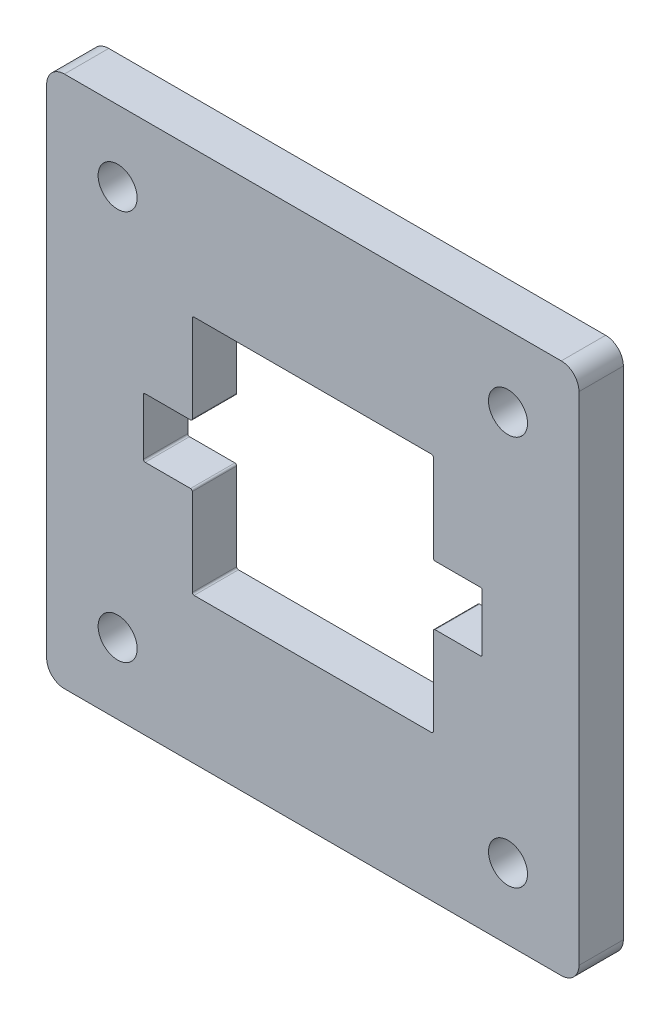
SolidWorks part; units mm, degrees
ref_plane "Front Plane" through (0, 0, 0) normal (0, 0, 1) x (1, 0, 0)
ref_plane "Top Plane" through (0, 0, 0) normal (0, 1, 0) x (1, 0, 0)
ref_plane "Right Plane" through (0, 0, 0) normal (1, 0, 0) x (0, 0, -1)
sketch "Sketch1" plane through (0, 0, 0) normal (0, 0, 1) x (1, 0, 0)
  line L0 (10.425, 10.425) -> (10.425, 16.925)
  line L1 (10.425, 16.925) -> (6.925, 16.925)
  line L2 (6.925, 16.925) -> (6.925, 21.175)
  line L3 (6.925, 21.175) -> (10.425, 21.175)
  line L4 (10.425, 21.175) -> (10.425, 27.675)
  line L5 (10.425, 27.675) -> (27.675, 27.675)
  line L6 (27.675, 27.675) -> (27.675, 21.175)
  line L7 (27.675, 16.925) -> (31.175, 16.925)
  line L8 (31.175, 16.925) -> (31.175, 21.175)
  line L9 (27.675, 21.175) -> (31.175, 21.175)
  line L10 (27.675, 16.925) -> (27.675, 10.425)
  line L11 (27.675, 10.425) -> (10.425, 10.425)
  line L12 (19.05, 27.675) -> (19.05, 10.425) construction
  line L13 (31.175, 19.05) -> (6.925, 19.05) construction
  line L14 (19.05, 38.1) -> (19.05, 0) construction
  line L15 (0, 0) -> (38.1, 0)
  line L16 (0, 0) -> (0, 38.1)
  line L17 (0, 38.1) -> (38.1, 38.1)
  line L18 (38.1, 0) -> (38.1, 38.1)
  line L19 (38.1, 19.05) -> (0, 19.05) construction
  point P17 (19.05, 19.05)
  point P18 (19.05, 19.05)
  dimension "D1" = 17.25
  dimension "D2" = 17.25
  dimension "D3" = 24.25
  dimension "D4" = 4.25
  dimension "D5" = 38.1
  dimension "D6" = 38.1
extrude "Boss-Extrude1" add sketch "Sketch1" along normal blind 3.175
fillet "Fillet1" radius 1.27 4 edges at (0, 0, 1.5875) (38.1, 0, 1.5875) (38.1, 38.1, 1.5875) (0, 38.1, 1.5875)
fillet "Fillet2" radius 0.127 12 edges at (10.425, 10.425, 1.5875) (31.175, 16.925, 1.5875) (27.675, 10.425, 1.5875) (27.675, 16.925, 1.5875) (31.175, 21.175, 1.5875) (27.675, 21.175, 1.5875) (27.675, 27.675, 1.5875) (10.425, 27.675, 1.5875) (10.425, 21.175, 1.5875) (6.925, 21.175, 1.5875) (6.925, 16.925, 1.5875) (10.425, 16.925, 1.5875)
hole_wizard "#3 Clearance Hole1" positions "Sketch2" profile "Sketch3" hole size "#3" standard "ANSI Inch" end condition through all
sketch "Sketch2" plane through (0, 0, 3.175) normal (0, 0, 1) x (1, 0, 0)
  line L1 (5.08, 33.02) -> (33.02, 33.02) construction
  line L2 (33.02, 33.02) -> (33.02, 5.08) construction
  line L3 (33.02, 19.05) -> (38.1, 19.05) construction
  line L4 (38.1, 1.27) -> (38.1, 36.83) construction
  line L7 (19.05, 33.02) -> (19.05, 38.1) construction
  line L8 (36.83, 38.1) -> (1.27, 38.1) construction
  point P0 (5.08, 33.02)
  point P2 (33.02, 33.02)
  point P4 (33.02, 5.08)
  point P6 (5.08, 5.08)
  dimension "D1" = 27.94
  dimension "D2" = 27.94
sketch "Sketch3" plane through (5.08, 33.02, 3.175) normal (1, 0, 0) x (0, -1, 0)
  line L0 (0, 0) -> (0, 3.175)
  line L1 (0, 3.175) -> (1.397, 3.175)
  line L2 (1.397, 3.175) -> (1.397, 0)
  line L5 (1.397, 0) -> (0, 0)
  line L11 (0, -6.35) -> (0, 107.95) construction
  dimension "Thru Hole Dia." = 2.794
  dimension "Thru Hole Depth" = 3.175
